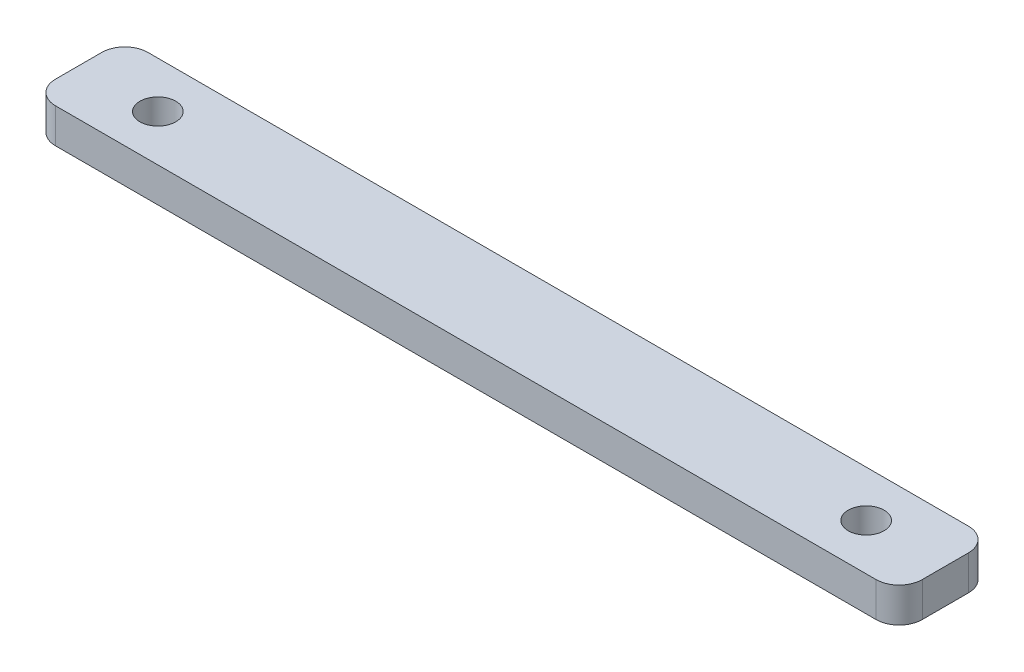
SolidWorks part; units mm, degrees
ref_plane "前视基准面" through (0, 0, 0) normal (0, 0, 1) x (1, 0, 0)
ref_plane "上视基准面" through (0, 0, 0) normal (0, 1, 0) x (1, 0, 0)
ref_plane "右视基准面" through (0, 0, 0) normal (1, 0, 0) x (0, 0, -1)
sketch "草图1" plane through (0, 0, 0) normal (0, 1, 0) x (1, 0, 0)
  line L0 (0, 0) -> (0, -20.3363) construction
  line L1 (37.5, 4) -> (-37.5, 4)
  line L2 (37.5, 4) -> (37.5, -4)
  line L3 (37.5, -4) -> (-37.5, -4)
  line L4 (-37.5, 4) -> (-37.5, -4)
  line L5 (37.5, 4) -> (-37.5, -4) construction
  line L6 (37.5, -4) -> (-37.5, 4) construction
  line L7 (0, 0) -> (-51.4538, 0) construction
  circle A0 centre (-30.645, 0) radius 1.55
  circle A1 centre (30.645, 0) radius 1.55
  point P0 (0, 0)
  dimension "D1" = 3.1
  dimension "D2" = 3.1
  dimension "D3" = 61.29
  dimension "D4" = 8
  dimension "D5" = 75
extrude "凸台-拉伸1" add sketch "草图1" along normal blind 3
fillet "圆角1" radius 2 4 edges at (37.5, 1.5, 4) (37.5, 1.5, -4) (-37.5, 1.5, -4) (-37.5, 1.5, 4)
